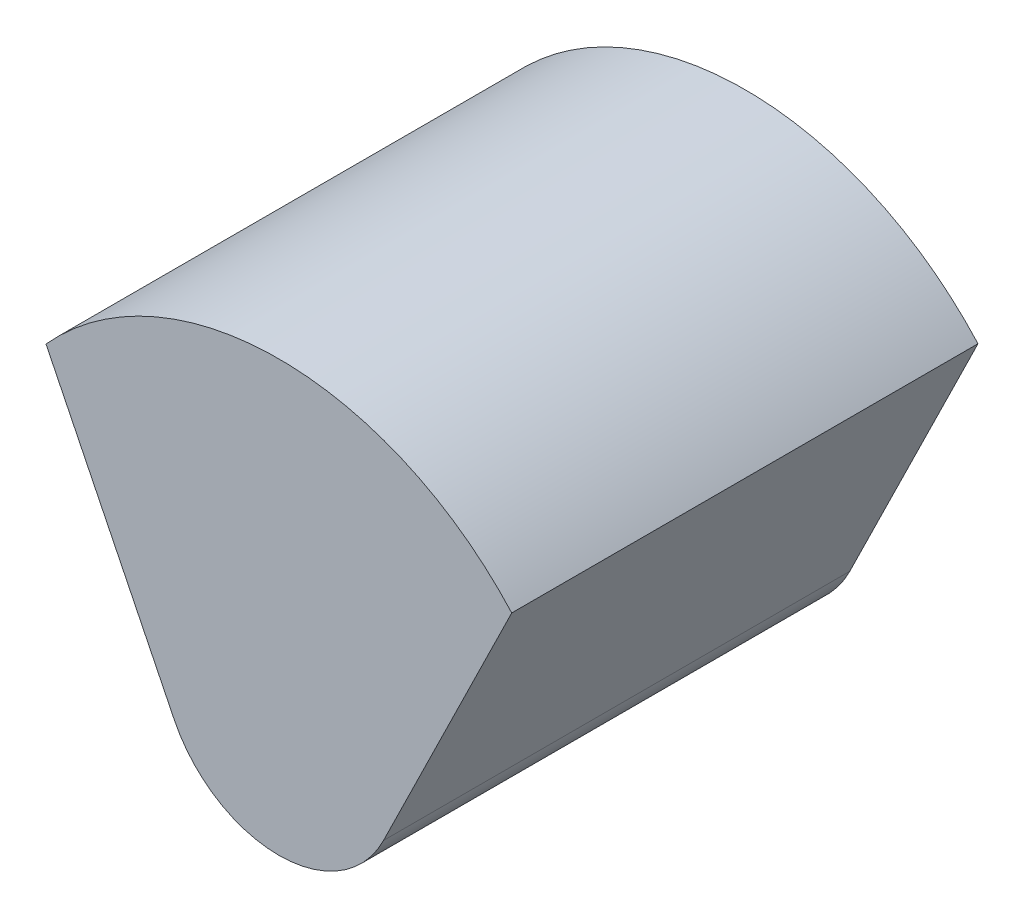
SolidWorks part; units mm, degrees
material "BUTYL"
ref_plane "Plan de face" through (0, 0, 0) normal (0, 0, 1) x (1, 0, 0)
ref_plane "Plan de dessus" through (0, 0, 0) normal (0, 1, 0) x (1, 0, 0)
ref_plane "Plan de droite" through (0, 0, 0) normal (1, 0, 0) x (0, 0, -1)
ref_plane "Plan1" through (0, 0, 6) normal (0, 0, 1) x (1, 0, 0)
sketch "Esquisse1" plane through (0, 0, 6) normal (0, 0, 1) x (1, 0, 0)
  line L0 (-52.3697, 0) -> (54.1422, 0) construction
  line L1 (-24.0095, 17) -> (19.4976, 17) construction
  line L2 (0, -6.3649) -> (0, 23.4455) construction
  line L3 (1.72, 23.4455) -> (1.72, 5.7204) construction
  line L4 (0.8224, 14.7593) -> (-0.2778, 17)
  line L5 (2.6176, 14.7593) -> (3.7178, 17)
  arc A0 (0.8224, 14.7593) -> (2.6176, 14.7593) centre (1.72, 15.2) ccw
  arc A1 (3.7178, 17) -> (-0.2778, 17) centre (1.72, 15.2) ccw
  dimension "D4" = 2
  dimension "D1" = 17
  dimension "D2" = 1.72
  dimension "D3" = 1.8
  dimension "D5" = 52.3
extrude "Boss.-Extru.1" add sketch "Esquisse1" against normal blind 4
